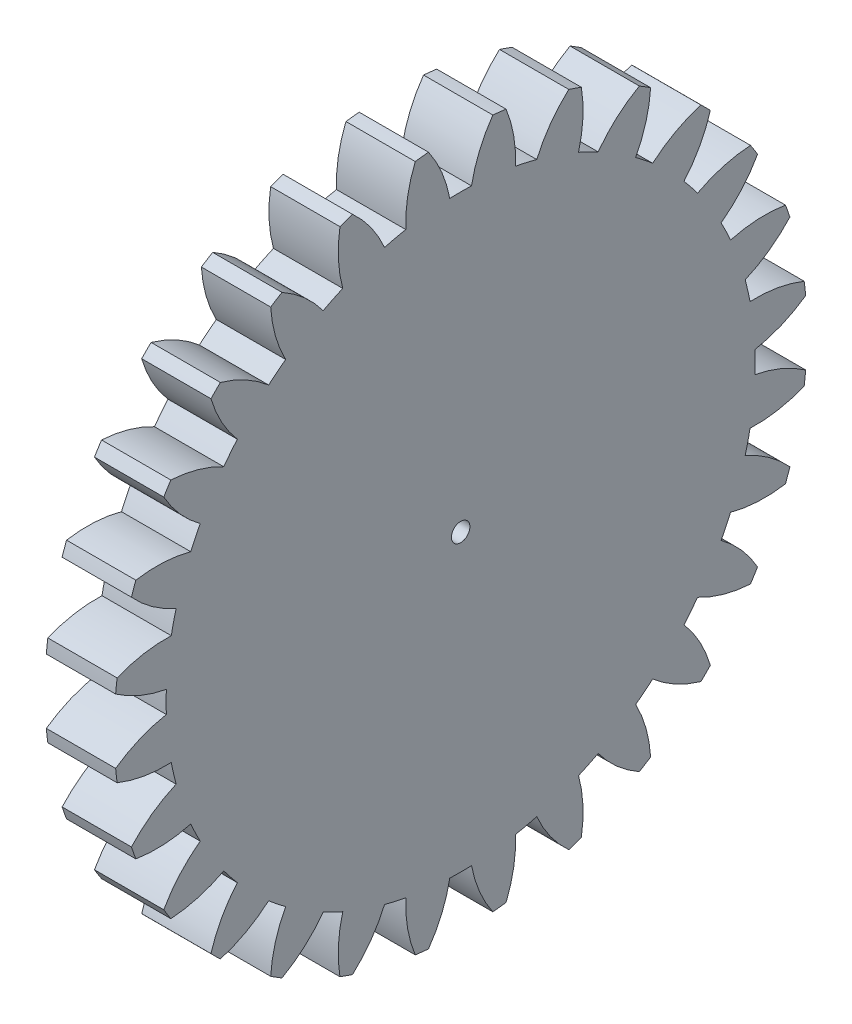
SolidWorks part; units mm, degrees
material "PET"
ref_plane "Plane1" through (0, 0, 0) normal (0, 0, 1) x (1, 0, 0)
ref_plane "Plane2" through (0, 0, 0) normal (0, 1, 0) x (1, 0, 0)
ref_plane "Plane3" through (0, 0, 0) normal (1, 0, 0) x (0, 0, -1)
sketch "HoldingSke" plane through (0, 0, 0) normal (0, 1, 0) x (1, 0, 0)
  line L0 (0, 0) -> (0.8829, -0.4695)
  line L1 (-15, 0) -> (100, 0) construction
  line L2 (0, 0) -> (-2.1039, 2.3779)
  line L3 (0, 0) -> (-11.863, 4.5341)
  line L4 (0, 0) -> (7.6251, 4.0544)
  line L5 (0, 0) -> (-46.8476, -17.4728)
  line L6 (0, 0) -> (-2.4869, -1.6779)
  line L7 (-2.1039, 2.3779) -> (8.6586, 51.2059)
  line L8 (-76.2, 54.61) -> (-76.1, 54.61)
  line L9 (-71.009, 38.7566) -> (-53.1078, 45.2721)
  line L10 (-76.2, 71.12) -> (104.1128, 71.12)
  line L11 (0, 0) -> (-3, 0)
  line L12 (-76.2, 101.6) -> (-76.162, 101.6)
  line L13 (24.9733, 27.94) -> (52.9518, 28.4284)
  line L14 (24.9733, 27.94) -> (24.9743, 27.94)
  line L15 (24.9733, 27.94) -> (100.4006, 29.5858)
  line L16 (-63.627, -1) -> (-12.827, -1)
  circle A0 centre (0, 0) radius 0.4
  circle A1 centre (0, 0) radius 12.749
  circle A2 centre (0, 0) radius 37.5
  circle A3 centre (0, 0) radius 0.4
  dimension "MHD" = 25.498
  dimension "Hub_dia" = 75
  dimension "Bore" = 0.8
  dimension "MBD" = 0.8
  dimension "Num_teeth" = 28
  dimension "Pitch" = 1
  dimension "Overall_len" = 50
  dimension "Show_teeth" = 28
  dimension "Thickness" = 3
  dimension "OAL" = 50.0001
  dimension "T_dim" = 0.1
  dimension "Ap" = 20
  dimension "H" = 19.05
  dimension "Pitch_radius" = 180.3128
  dimension "Width" = 3
  dimension "Backlash" = 0.038
  dimension "Addendum_fac" = 1
  dimension "Dedendum_fac" = 1.25
  dimension "Clearance_fac" = 0.25
  dimension "Dedendum_add" = 0.001
  dimension "Module" = 1
sketch "BasProSke" plane through (0, 0, 0) normal (0, 1, 0) x (1, 0, 0)
  line L0 (-10, 0) -> (60, 0) construction
  line L1 (0, 0) -> (0, 15)
  line L2 (0, 0) -> (3, 0)
  line L3 (3, 0) -> (3, 15)
  line L4 (3, 15) -> (0, 15)
  dimension "Thickness" = 3
  dimension "Diameter" = 30
revolve "Base-Revolve" add sketch "BasProSke" angle 360 about L0
sketch "TooCutSke" plane through (0, 0, 0) normal (1, 0, 0) x (0, 0, -1)
  line L1 (0, 0) -> (0, 107) construction
  line L2 (0, 0) -> (-0.8515, 13.9741) construction
  line L3 (0, 0) -> (-3.1309, 27.7873) construction
  line L4 (-0.8515, 13.9741) -> (-1.5654, 13.8936) construction
  arc A0 (0.4713, 12.7403) -> (-0.4713, 12.7403) centre (0, 0) ccw
  arc A1 (1.4098, 14.9591) -> (-1.4098, 14.9591) centre (0, 0) ccw
  circle A2 centre (0, 0) radius 14 construction
  circle A3 centre (0, 0) radius 13.1557 construction
  arc A4 (-0.4713, 12.7403) -> (-1.4098, 14.9591) centre (-5.9775, 11.7193) ccw
  arc A5 (1.4098, 14.9591) -> (0.4713, 12.7403) centre (5.9775, 11.7193) ccw
  dimension "Root_dia" = 25.498
  dimension "Overcut_dia" = 30.0508
  dimension "Pitch_dia" = 28
  dimension "Base_dia" = 26.3114
  dimension "Flank_rad" = 5.6
  dimension "Half_ang" = 6.429
  dimension "Half_CT" = 0.7185
extrude "ToothCut" cut sketch "TooCutSke" along normal through all
fillet "Breaks" [suppressed] radius 0.02
fillet "RootFillets" [suppressed] radius 0.251
pattern_circular "TeethCuts" count 28 every 12.857 about axis through (-10, 0, 0) along (1, 0, 0) of "ToothCut", "RootFillets", "Breaks"
sketch "HubNeaOneSke" plane through (0, 0, 0) normal (-1, 0, 0) x (0, 0, 1)
  circle A0 centre (0, 0) radius 12.749
  dimension "Diameter" = 25.498
extrude "HubNearOne" [suppressed] add sketch "HubNeaOneSke" along normal blind 47.0001
sketch "HubNeaBotSke" plane through (0, 0, 0) normal (-1, 0, 0) x (0, 0, 1)
  circle A0 centre (0, 0) radius 12.749
  dimension "Diameter" = 25.498
extrude "HubNearBoth" [suppressed] add sketch "HubNeaBotSke" along normal blind 23.5
ref_plane "FarPln" through (3, 0, 0) normal (1, 0, 0) x (0, 0, -1)
sketch "HubFarSke" plane through (3, 0, 0) normal (1, 0, 0) x (0, 0, -1)
  circle A0 centre (0, 0) radius 12.749
  dimension "Diameter" = 25.498
extrude "HubFar" [suppressed] add sketch "HubFarSke" along normal blind 23.5
sketch "BorSke" plane through (0, 0, 0) normal (1, 0, 0) x (0, 0, -1)
  circle A0 centre (0, 0) radius 0.4
  dimension "Diameter" = 0.8
extrude "Bore" cut sketch "BorSke" along normal mid plane 100.0001
sketch "KeySke" plane through (0, 0, 0) normal (1, 0, 0) x (0, 0, -1)
  line L0 (-0.05, 0) -> (-0.05, 0.5)
  line L1 (-0.05, 0.5) -> (0.05, 0.5)
  line L2 (0.05, 0.5) -> (0.05, 0)
  line L3 (0, 0) -> (0, 34) construction
  line L4 (-0.05, 0) -> (0.05, 0)
  dimension "Offset" = 0.5
  dimension "Width" = 0.1
extrude "Keyway" [suppressed] cut sketch "KeySke" along normal mid plane 100.0001
pattern_circular "Keyway2" [suppressed] count 2 every 90 about axis through (-10, 0, 0) along (1, 0, 0)
sketch "Эскиз1" plane through (3, 0, 0) normal (1, 0, 0) x (0, 0, -1)
  circle A0 centre (0, 0) radius 3.3946
  dimension "D1" = 6.7892
equation "' \"Module@HoldingSke\" = 6.35"
equation "' \"Num_teeth@HoldingSke\" = 12"
equation "' \"Ap@HoldingSke\" =  20"
equation "' \"Ap@HoldingSke\" = 20"
equation "' \"Width@HoldingSke\" = 0.5 * 25.4"
equation "' \"Hub_dia@HoldingSke\"= 1 * 25.4"
equation "' \"Hub_dia@HoldingSke\" = 1 * 25.4"
equation "' \"Overall_len@HoldingSke\" = 1.0 * 25.4"
equation "' \"Bore@HoldingSke\" = 0.75 * 25.4"
equation "' \"T_dim@HoldingSke\" = 0.1 * 25.4"
equation "' \"Width@KeySke\" = 0.25 * 25.4"
equation "' \"Show_teeth@HoldingSke\" = 13"
equation "' \"Backlash@HoldingSke\" = 0.009 * 25.4"
equation "' \"Addendum_fac@HoldingSke\" = 1.0"
equation "' \"Dedendum_fac@HoldingSke\" = 1.25"
equation "' \"Dedendum_add@HoldingSke\" = 0.00005 * 25.4"
equation "' \"Clearance_fac@HoldingSke\" = 0.25"
equation "\"Pitch@HoldingSke\" = 1 / \"Module@HoldingSke\""
equation "\"Overcut_dia@TooCutSke\" = (\"Num_teeth@HoldingSke\" + 2 * \"Addendum_fac@HoldingSke\") / \"Pitch@HoldingSke\" + 0.002 * 25.4"
equation "\"Pitch_dia@TooCutSke\" = \"Num_teeth@HoldingSke\" / \"Pitch@HoldingSke\""
equation "\"Base_dia@TooCutSke\" = \"Num_teeth@HoldingSke\" / \"Pitch@HoldingSke\" * cos((\"Ap@HoldingSke\"  * 3.14159265 / 180))"
equation "\"Root_dia@TooCutSke\" = (\"Num_teeth@HoldingSke\" + 2) / \"Pitch@HoldingSke\" - 2 * (\"Addendum_fac@HoldingSke\" + \"Dedendum_fac@HoldingSke\") / \"Pitch@HoldingSke\" - \"Dedendum_add@HoldingSke\" * 2"
equation "\"Half_ang@TooCutSke\" = 180 / \"Num_teeth@HoldingSke\""
equation "\"Half_CT@TooCutSke\" = \"Num_teeth@HoldingSke\" / \"Pitch@HoldingSke\" * sin((3.14159265 / 2 / \"Num_teeth@HoldingSke\")) / 2 - 7 * \"Backlash@HoldingSke\" / 4"
equation "\"Flank_rad@TooCutSke\" = \"Num_teeth@HoldingSke\" / \"Pitch@HoldingSke\" / 5"
equation "\"Radius@RootFillets\" = \"Clearance_fac@HoldingSke\" / \"Pitch@HoldingSke\" + \"Dedendum_add@HoldingSke\""
equation "\"Break_rad@Breaks\" = 0.02 / \"Pitch@HoldingSke\""
equation "\"Thickness@HoldingSke\" = \"Width@HoldingSke\""
equation "\"OAL@HoldingSke\" = \"Thickness@HoldingSke\""
equation "\"MHD@HoldingSke\" = (\"Num_teeth@HoldingSke\" + 2) / \"Pitch@HoldingSke\" - 2 * (\"Addendum_fac@HoldingSke\" + \"Dedendum_fac@HoldingSke\")  / \"Pitch@HoldingSke\" - \"Dedendum_add@HoldingSke\" * 2"
equation "\"MBD@HoldingSke\" = (\"Num_teeth@HoldingSke\" + 2) / \"Pitch@HoldingSke\" - 2 * (\"Addendum_fac@HoldingSke\" + \"Dedendum_fac@HoldingSke\")  / \"Pitch@HoldingSke\" - \"Dedendum_add@HoldingSke\" * 2 - 0.002 * 25.4"
equation "\"MHD@HoldingSke\" = ((sgn( \"MHD@HoldingSke\" - \"Hub_dia@HoldingSke\" )-1)*( \"MHD@HoldingSke\" - \"Hub_dia@HoldingSke\" ))/-2+ \"Hub_dia@HoldingSke\""
equation "\"MBD@HoldingSke\" = ((sgn( \"MBD@HoldingSke\" - \"Bore@HoldingSke\" )-1)*( \"MBD@HoldingSke\" - \"Bore@HoldingSke\" ))/-2+ \"Bore@HoldingSke\""
equation "\"OAL@HoldingSke\" = ((sgn( \"OAL@HoldingSke\" - \"Overall_len@HoldingSke\" )+1)*( \"OAL@HoldingSke\" - \"Overall_len@HoldingSke\" ))/2 + \"Overall_len@HoldingSke\" + 0.000002 * 25.4"
equation "\"Num_teeth@TeethCuts\" = int( \"Show_teeth@HoldingSke\" ) + 1"
equation "\"Num_teeth@TeethCuts\" = ((sgn( \"Num_teeth@TeethCuts\" - \"Num_teeth@HoldingSke\" )-1)*( \"Num_teeth@TeethCuts\" - \"Num_teeth@HoldingSke\" ))/-2+ \"Num_teeth@HoldingSke\""
equation "\"Num_teeth@TeethCuts\" = ((sgn( \"Num_teeth@TeethCuts\" - 2.0)+1)*( \"Num_teeth@TeethCuts\" - 2.0))/2 +2.0"
equation "\"Angle@TeethCuts\" = 360.0 / \"Num_teeth@HoldingSke\""
equation "\"Diameter@BasProSke\" = (\"Num_teeth@HoldingSke\" + 2 * \"Addendum_fac@HoldingSke\") / \"Pitch@HoldingSke\""
equation "\"Thickness@BasProSke\"  = \"Thickness@HoldingSke\""
equation "' \"Fillet_rad@BasProSke\" =  \"Thickness@HoldingSke\" * 0.05"
equation "' \"Fillet_rad@BasProSke\" = \"Thickness@HoldingSke\" * 0.05"
equation "\"MHD@HoldingSke\" = ((sgn( \"MHD@HoldingSke\" - \"Root_dia@TooCutSke\" )-1)*( \"MHD@HoldingSke\" - \"Root_dia@TooCutSke\" ))/-2+ \"Root_dia@TooCutSke\""
equation "\"Diameter@HubNeaOneSke\" = \"MHD@HoldingSke\""
equation "\"Length@HubNearOne\" = \"OAL@HoldingSke\" - \"Thickness@BasProSke\""
equation "\"Diameter@HubNeaBotSke\" = \"MHD@HoldingSke\""
equation "\"Length@HubNearBoth\" = ( \"OAL@HoldingSke\" - \"Thickness@BasProSke\" ) / 2.0"
equation "\"Thickness@FarPln\" = \"Thickness@BasProSke\""
equation "\"Diameter@HubFarSke\" = \"MHD@HoldingSke\""
equation "\"Length@HubFar\" = ( \"OAL@HoldingSke\" - \"Thickness@BasProSke\" ) / 2.0"
equation "\"Diameter@BorSke\" = \"MBD@HoldingSke\""
equation "\"D1@Bore\" = \"OAL@HoldingSke\" * 2.0"
equation "\"D1@Keyway\" = \"OAL@HoldingSke\" * 2.0"
equation "\"Offset@KeySke\" = \"T_dim@HoldingSke\" + \"MBD@HoldingSke\" / 2.0"
